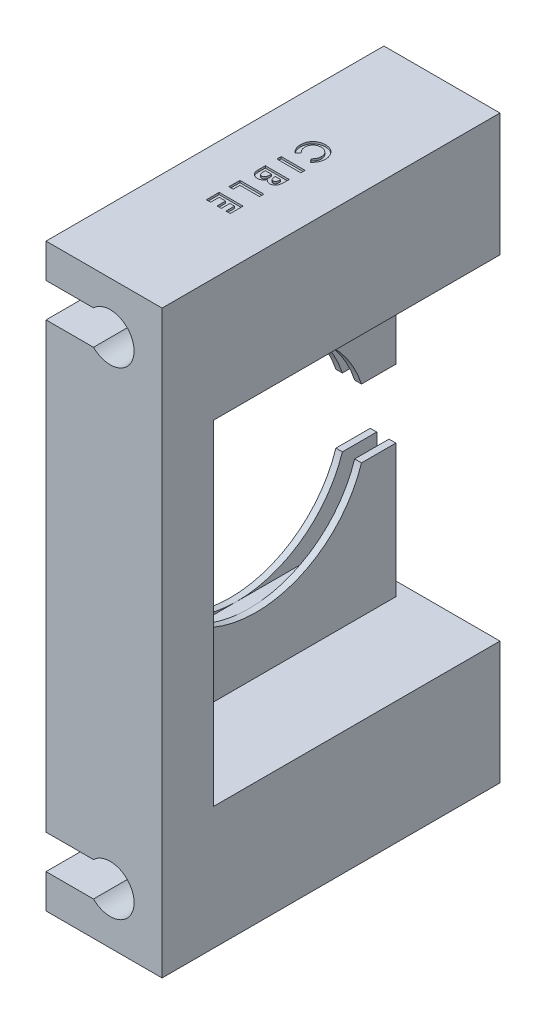
SolidWorks part; units mm, degrees
ref_plane "Plan de face" through (0, 0, 0) normal (0, 0, 1) x (1, 0, 0)
ref_plane "Plan de dessus" through (0, 0, 0) normal (0, 1, 0) x (1, 0, 0)
ref_plane "Plan de droite" through (0, 0, 0) normal (1, 0, 0) x (0, 0, -1)
sketch "Esquisse1" plane through (0, 0, 0) normal (0, 0, 1) x (1, 0, 0)
  line L1 (-8.5, -42.5) -> (8.5, -42.5)
  line L2 (-8.5, -42.5) -> (-8.5, 42.5)
  line L3 (-8.5, 42.5) -> (8.5, 42.5)
  line L4 (8.5, -42.5) -> (8.5, 42.5)
  line L5 (-8.5, -42.5) -> (8.5, 42.5) construction
  line L6 (-8.5, 42.5) -> (8.5, -42.5) construction
  point P0 (0, 0)
  dimension "D1" = 17
  dimension "D2" = 85
extrude "Boss.-Extru.1" add sketch "Esquisse1" along normal blind 49.5
sketch "Esquisse2" plane through (0, 0, 0) normal (0, 0, -1) x (-1, 0, 0)
  line L0 (8.5, 42.5) -> (8.5, -42.5) construction
  line L5 (7.55, 16.25) -> (5.75, 16.25)
  line L6 (7.55, 16.25) -> (7.55, -16.25)
  line L7 (7.55, -16.25) -> (5.75, -16.25)
  line L8 (5.75, 16.25) -> (5.75, -16.25)
  line L9 (7.55, 16.25) -> (5.75, -16.25) construction
  line L10 (7.55, -16.25) -> (5.75, 16.25) construction
  point P0 (6.65, 0)
  dimension "D1" = 1.8
  dimension "D2" = 32.5
  dimension "D3" = 0.95
extrude "Enlèv. mat.-Extru.1" cut sketch "Esquisse2" against normal blind 38.5
sketch "Esquisse3" plane through (0, 0, 0) normal (0, 0, -1) x (-1, 0, 0)
  line L0 (-8.5, -42.5) -> (-8.5, 42.5) construction
  line L1 (8.5, 24.5) -> (-8.5, 24.5)
  line L2 (8.5, 24.5) -> (8.5, -24.5)
  line L3 (8.5, -24.5) -> (-8.5, -24.5)
  line L4 (-8.5, 24.5) -> (-8.5, -24.5)
  line L5 (8.5, 24.5) -> (-8.5, -24.5) construction
  line L6 (8.5, -24.5) -> (-8.5, 24.5) construction
  point P0 (0, 0)
  dimension "D1" = 49
extrude "Enlèv. mat.-Extru.2" cut sketch "Esquisse3" against normal blind 2
sketch "Esquisse4" plane through (-8.5, 0, 0) normal (-1, 0, 0) x (0, 0, 1)
  line L0 (2, -24.5) -> (2, 24.5) construction
  circle A0 centre (22.5, 0) radius 16.25
  dimension "D1" = 32.5
  dimension "D2" = 20.5
extrude "Enlèv. mat.-Extru.3" cut sketch "Esquisse4" against normal through all
sketch "Esquisse5" plane through (-8.5, 0, 0) normal (-1, 0, 0) x (0, 0, 1)
  line L0 (7.0384, -5) -> (2, -5)
  line L1 (2, -24.5) -> (2, 24.5) construction
  line L2 (2, -5) -> (2, 5)
  line L3 (2, 5) -> (7.0384, 5)
  line L4 (7.0384, 5) -> (7.0384, -5)
  line L5 (49.5, -42.5) -> (0, -42.5) construction
  circle A0 centre (22.5, 0) radius 16.25 construction
  dimension "D1" = 10
  dimension "D2" = 37.5
extrude "Enlèv. mat.-Extru.4" cut sketch "Esquisse5" against normal through all
sketch "Esquisse6" plane through (0, 0, 0) normal (0, 0, -1) x (-1, 0, 0)
  line L0 (8.5, -32.5) -> (1.55, -32.5)
  line L1 (8.5, -24.5) -> (8.5, -42.5) construction
  line L2 (8.5, -32.5) -> (8.5, -37.5)
  line L3 (8.5, -37.5) -> (1.55, -37.5)
  line L4 (8.5, -42.5) -> (-8.5, -42.5) construction
  line L5 (-2.04, 0) -> (3.9749, 0) construction
  line L6 (8.5, 32.5) -> (8.5, 37.5)
  line L7 (8.5, 32.5) -> (1.55, 32.5)
  line L8 (8.5, 37.5) -> (1.55, 37.5)
  arc A0 (1.55, -37.5) -> (1.55, -32.5) centre (-0.8995, -35) cw
  arc A1 (1.55, 37.5) -> (1.55, 32.5) centre (-0.8995, 35) ccw
  dimension "D1" = 3.5
  dimension "D2" = 5
  dimension "D3" = 6.95
  dimension "D4" = 6.95
  dimension "D5" = 5
extrude "Enlèv. mat.-Extru.5" cut sketch "Esquisse6" against normal through all
sketch "Esquisse7" plane through (8.5, 0, 0) normal (1, 0, 0) x (0, 0, -1)
  line L5 (-2, 24.5) -> (-42, 24.5)
  line L6 (-2, 24.5) -> (-2, -24.5)
  line L7 (-2, -24.5) -> (-42, -24.5)
  line L8 (-42, 24.5) -> (-42, -24.5)
  dimension "D1" = 49
  dimension "D2" = 40
extrude "Enlèv. mat.-Extru.7" cut sketch "Esquisse7" against normal blind 13.25
sketch "Esquisse8" plane through (0, 42.5, 0) normal (0, 1, 0) x (1, 0, 0)
  line L0 (-2, 0) -> (-2, -49.5) construction
  line L1 (8.5, 0) -> (-8.5, 0) construction
  line L2 (8.5, -49.5) -> (-8.5, -49.5) construction
  line L3 (8.5, -49.5) -> (8.5, 0) construction
  text T0 "<b>CIBLE</b>" font "Century Gothic" height 3.5
  dimension "D1" = 10.5
extrude "Enlèv. mat.-Extru.8" cut sketch "Esquisse8" against normal blind 0.3
